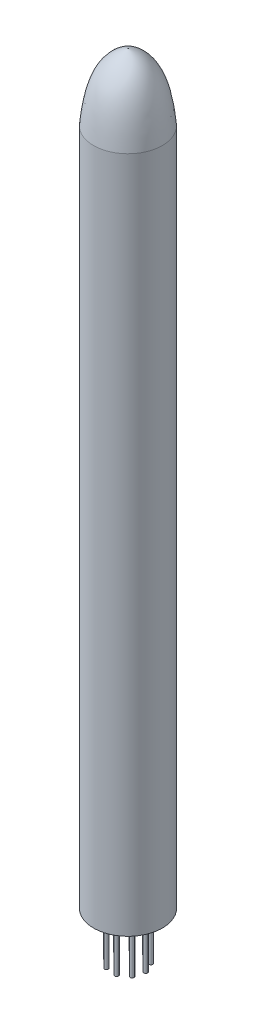
SolidWorks part; units mm, degrees
ref_plane "前视基准面" through (0, 0, 0) normal (0, 0, 1) x (1, 0, 0)
ref_plane "上视基准面" through (0, 0, 0) normal (0, 1, 0) x (1, 0, 0)
ref_plane "右视基准面" through (0, 0, 0) normal (1, 0, 0) x (0, 0, -1)
sketch "草图1" plane through (0, 0, 0) normal (0, 0, 1) x (1, 0, 0)
  line L0 (0, 8.2633) -> (0, -18.1051) construction
  line L1 (-3.6, 71) -> (-3.6, 0)
  line L2 (-3.6, 0) -> (0, 0)
  line L3 (0, 0) -> (0, 78)
  spline S0 degree 3 poles (-3.6, 71) (-3.3379, 73.5517) (-2.9316, 77.0763) (0, 78) knots 0 0 0 0 1 1 1 1
  point P8 (-3.6, 60.5999)
  point P11 (-3.6, 60.5999)
  dimension "D1" = 0
  dimension "D2" = 3.6
  dimension "D3" = 3.6
  dimension "D4" = 71
  dimension "D7" = 7
revolve "旋转1" add sketch "草图1" angle 360 about L0
sketch "草图2" plane through (0, 0, 0) normal (0, -1, 0) x (1, 0, 0)
  circle A0 centre (-0.9878, -1.3835) radius 0.2
  dimension "D1" = 1.7
extrude "凸台-拉伸1" add sketch "草图2" along normal blind 5
sketch "草图4" plane through (0, 0, 0) normal (0, 0, 1) x (1, 0, 0)
  line L0 (0, -7.1561) -> (0, 7.2304) construction
  dimension "D1" = 0
pattern_circular "阵列(圆周)1" count 9 over 360 about axis through (0, 0, 0) along (0, 1, 0) of "凸台-拉伸1"
